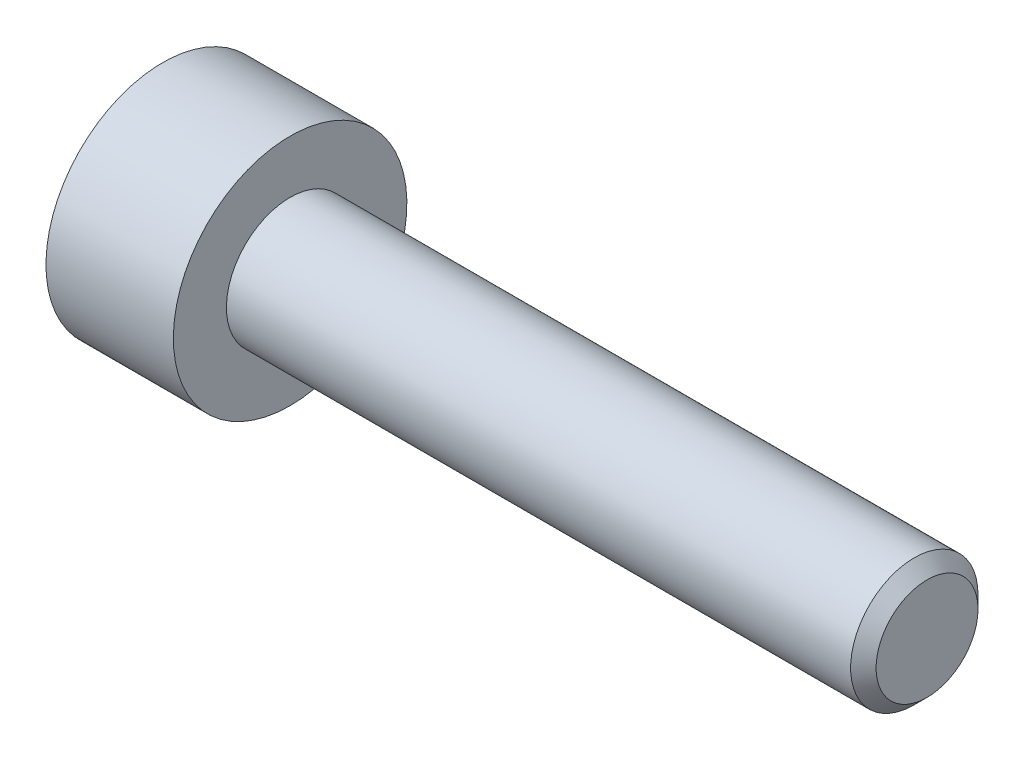
SolidWorks part; units mm, degrees
material "Plain Carbon Steel"
ref_plane "Front Plane" through (0, 0, 0) normal (0, 0, 1) x (1, 0, 0)
ref_plane "Top Plane" through (0, 0, 0) normal (0, 1, 0) x (1, 0, 0)
ref_plane "Right Plane" through (0, 0, 0) normal (1, 0, 0) x (0, 0, -1)
sketch "Sketch2" plane through (0, 0, 0) normal (1, 0, 0) x (0, 0, -1)
  circle A0 centre (0, 0) radius 1.5
  dimension "D1" = 3
extrude "Boss-Extrude1" add sketch "Sketch2" against normal blind 15
chamfer "Chamfer1" distance 0.3 angle 45 1 edges at (0, 0, -1.5)
sketch "Sketch6" plane through (0, 0, 0) normal (0, 0, 1) x (1, 0, 0)
  line L0 (-18, 0) -> (-18, 2.75)
  line L1 (-18, 0) -> (-15, 0)
  line L2 (-18, 2.75) -> (-15, 2.75)
  line L6 (-15, 2.75) -> (-15, 0)
  line L8 (-15, 0) -> (-14.6471, 0) construction
  line L10 (-15, 1.5) -> (-15, -1.5) construction
  dimension "D1" = 3
  dimension "D2" = 5.5
revolve "Revolve1" add sketch "Sketch6" angle 360 about L8
sketch "Sketch7" plane through (-18, 0, 0) normal (-1, 0, 0) x (0, 0, 1)
  line L1 (0, 1.4434) -> (-1.25, 0.7217)
  line L2 (-1.25, 0.7217) -> (-1.25, -0.7217)
  line L3 (-1.25, -0.7217) -> (0, -1.4434)
  line L4 (0, -1.4434) -> (1.25, -0.7217)
  line L5 (1.25, -0.7217) -> (1.25, 0.7217)
  line L6 (1.25, 0.7217) -> (0, 1.4434)
  circle A0 centre (0, 0) radius 1.25 construction
  dimension "D1" = 2.5
extrude "Cut-Extrude1" cut sketch "Sketch7" against normal blind 1.6
sketch "Sketch8" plane through (-18, 0, 0) normal (-1, 0, 0) x (0, 0, 1)
  circle A0 centre (0, 0) radius 1.4934
  dimension "D1" = 0.05
extrude "Cut-Extrude2" cut sketch "Sketch8" against normal blind 1 draft 45
